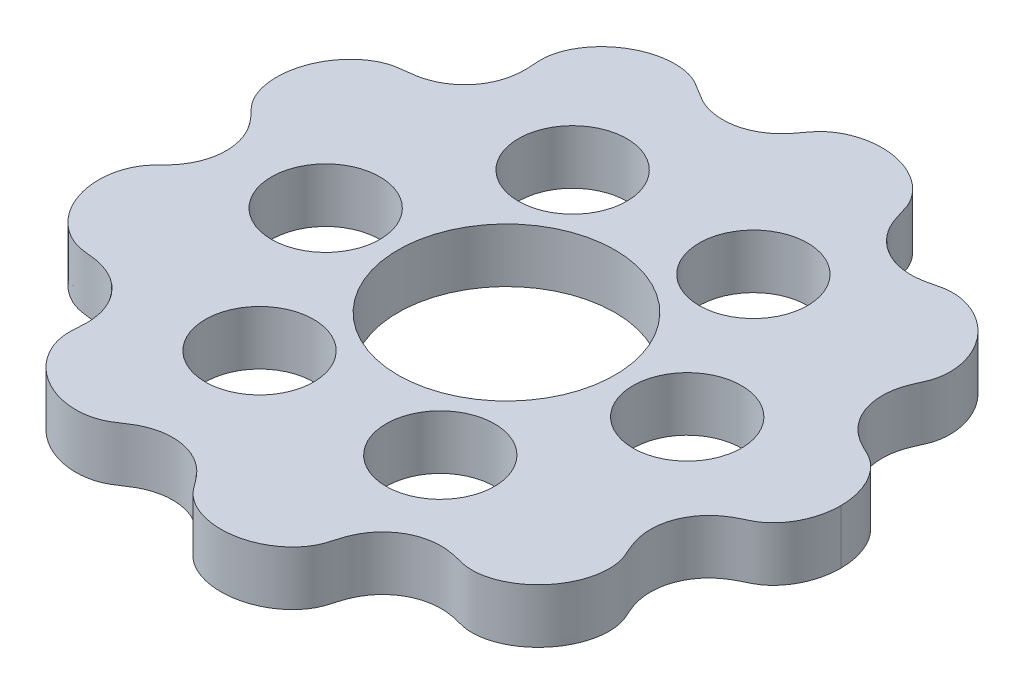
SolidWorks part; units mm, degrees
ref_plane "前视基准面" through (0, 0, 0) normal (0, 0, 1) x (1, 0, 0)
ref_plane "上视基准面" through (0, 0, 0) normal (0, 1, 0) x (1, 0, 0)
ref_plane "右视基准面" through (0, 0, 0) normal (1, 0, 0) x (0, 0, -1)
sketch "草图1" plane through (0, 0, 0) normal (0, 1, 0) x (1, 0, 0)
  circle A0 centre (10, 0) radius 3
  circle A1 centre (5, 8.6603) radius 3
  circle A2 centre (-5, 8.6603) radius 3
  circle A3 centre (-10, 0) radius 3
  circle A4 centre (-5, -8.6603) radius 3
  circle A5 centre (5, -8.6603) radius 3
  circle A6 centre (0, 0) radius 6
  spline S2 degree 3 poles (-15.5, 0.011) (-15.4991, -0.2474) (-15.5295, -0.4891) (-15.6305, -0.9323) (-15.6966, -1.1169) (-15.8274, -1.4223) (-15.8941, -1.5468) (-16.0615, -1.8321) (-16.1502, -1.9501) (-16.294, -2.1344) (-16.35, -2.199) (-16.4452, -2.3062) (-16.4827, -2.3465) (-16.549, -2.4168) (-16.5763, -2.4451) (-16.6255, -2.4958) (-16.6468, -2.5176) (-16.6852, -2.557) (-16.7027, -2.575) (-16.7501, -2.6239) (-16.7768, -2.6517) (-16.8523, -2.7322) (-16.8929, -2.7778) (-16.9689, -2.8679) (-17.0036, -2.9118) (-17.1158, -3.0628) (-17.1867, -3.1746) (-17.316, -3.4165) (-17.3739, -3.5459) (-17.5237, -3.9556) (-17.591, -4.2567) (-17.6669, -5.0909) (-17.6056, -5.6442) (-17.2735, -6.6868) (-17.0025, -7.1771) (-16.3143, -7.9884) (-15.8962, -8.3081) (-15.4173, -8.5299) (-15.3617, -8.5536) (-15.195, -8.6185) (-15.0848, -8.6534) (-14.9332, -8.6908) (-14.8937, -8.6996) (-14.7719, -8.7239) (-14.6902, -8.7368) (-14.5398, -8.7544) (-14.4959, -8.7591) (-14.3852, -8.7703) (-14.3217, -8.7762) (-14.1648, -8.7937) (-14.0931, -8.8018) (-13.932, -8.8263) (-13.8638, -8.8374) (-13.704, -8.87) (-13.6223, -8.8882) (-13.4132, -8.9463) (-13.292, -8.9838) (-12.9849, -9.1087) (-12.8028, -9.1943) (-12.4559, -9.4177) (-12.3042, -9.5314) (-12.0615, -9.7543) (-11.9646, -9.8547) (-11.7359, -10.1278) (-11.6244, -10.2932) (-11.4606, -10.5864) (-11.4015, -10.7131) (-11.3083, -10.9448) (-11.273, -11.0515) (-11.2007, -11.3042) (-11.1742, -11.4381) (-11.1285, -11.7253) (-11.1198, -11.8584) (-11.1107, -12.0688) (-11.1111, -12.1512) (-11.1135, -12.2864) (-11.1159, -12.342) (-11.1205, -12.4352) (-11.1231, -12.4758) (-11.1301, -12.58) (-11.1341, -12.6324) (-11.1439, -12.7633) (-11.1479, -12.8232) (-11.1534, -12.9331) (-11.1548, -12.9808) (-11.156, -13.1242) (-11.1523, -13.2129) (-11.1356, -13.3933) (-11.1226, -13.4837) (-11.0612, -13.7976) (-10.9881, -14.0267) (-10.6784, -14.7131) (-10.3504, -15.1578) (-9.529, -15.8895) (-9.036, -16.1775) (-7.9943, -16.5344) (-7.4449, -16.6024) (-6.7604, -16.5419) (-6.5865, -16.5121) (-6.3591, -16.4535) (-6.2975, -16.4355) (-6.1171, -16.3761) (-6.0036, -16.33) (-5.8229, -16.2417) (-5.7542, -16.2045) (-5.633, -16.1316) (-5.584, -16.1006) (-5.4817, -16.0328) (-5.4341, -16.0003) (-5.3255, -15.9263) (-5.275, -15.8917) (-5.1589, -15.8157) (-5.1072, -15.7823) (-4.9698, -15.699) (-4.8834, -15.6482) (-4.6836, -15.547) (-4.5837, -15.4995) (-4.3435, -15.4044) (-4.1963, -15.3526) (-3.8767, -15.2751) (-3.72, -15.2458) (-3.3969, -15.2164) (-3.2407, -15.212) (-2.961, -15.2265) (-2.8373, -15.2397) (-2.4558, -15.3046) (-2.2224, -15.376) (-1.8022, -15.5518) (-1.6312, -15.6488) (-1.352, -15.8308) (-1.2404, -15.9182) (-0.985, -16.1351) (-0.8834, -16.2441) (-0.7254, -16.4194) (-0.6714, -16.4862) (-0.582, -16.5991) (-0.5488, -16.6431) (-0.491, -16.7209) (-0.468, -16.7526) (-0.4265, -16.81) (-0.4087, -16.8347) (-0.3765, -16.8794) (-0.3618, -16.8998) (-0.322, -16.9548) (-0.299, -16.9861) (-0.2564, -17.0429) (-0.237, -17.0683) (-0.1638, -17.1612) (-0.1143, -17.219) (-0.0103, -17.3308) (0.0434, -17.3838) (0.2374, -17.5597) (0.3928, -17.6747) (0.7375, -17.8804) (0.9261, -17.9706) (1.5922, -18.2172) (2.1194, -18.3002) (3.1771, -18.2588) (3.7076, -18.1351) (4.6649, -17.7078) (5.0915, -17.4031) (5.5212, -16.9383) (5.6155, -16.8203) (5.7354, -16.646) (5.7702, -16.5915) (5.8676, -16.4271) (5.9228, -16.3173) (5.9973, -16.139) (6.0215, -16.0748) (6.0627, -15.9515) (6.0794, -15.8976) (6.113, -15.7821) (6.1275, -15.7306) (6.162, -15.6081) (6.179, -15.5474) (6.2207, -15.4107) (6.2402, -15.3484) (6.2947, -15.1912) (6.3299, -15.0936) (6.4211, -14.8872) (6.4615, -14.8015) (6.5729, -14.5951) (6.6517, -14.4617) (6.847, -14.1957) (6.9499, -14.07) (7.1828, -13.836) (7.3014, -13.7312) (7.5274, -13.5618) (7.6311, -13.4925) (7.9663, -13.2977) (8.1905, -13.2036) (8.6556, -13.0602) (8.8709, -13.0254) (9.2324, -12.9902) (9.3796, -12.9899) (9.6193, -12.9983) (9.7194, -13.0078) (10.0086, -13.0421) (10.1314, -13.0698) (10.321, -13.1117) (10.3859, -13.128) (10.4962, -13.1557) (10.5393, -13.1668) (10.6723, -13.2004) (10.7362, -13.2157) (10.8574, -13.2418) (10.9113, -13.2519) (11.0742, -13.2778) (11.1792, -13.288) (11.3968, -13.296) (11.5081, -13.2935) (11.9671, -13.2559) (12.3335, -13.1635) (13.0433, -12.8551) (13.3861, -12.6398) (13.9997, -12.1127) (14.2707, -11.801) (14.7616, -11.0354) (14.9524, -10.5646) (15.1204, -9.7223) (15.1321, -9.3512) (15.0759, -8.9387) (15.0625, -8.8639) (15.0246, -8.6928) (14.9982, -8.5985) (14.9438, -8.4395) (14.9201, -8.3771) (14.8708, -8.2589) (14.8495, -8.21) (14.8004, -8.1005) (14.7755, -8.0461) (14.7248, -7.9318) (14.7042, -7.885) (14.6611, -7.7823) (14.6379, -7.7257) (14.5844, -7.5842) (14.5512, -7.4925) (14.4889, -7.2807) (14.4607, -7.1748) (14.4095, -6.9133) (14.384, -6.7472) (14.3694, -6.4088) (14.3707, -6.2569) (14.4022, -5.933) (14.4299, -5.7674) (14.5013, -5.489) (14.5373, -5.3743) (14.6229, -5.1485) (14.6706, -5.042) (14.8248, -4.7398) (14.9458, -4.5587) (15.1751, -4.2675) (15.2842, -4.1535) (15.5238, -3.9267) (15.6387, -3.8381) (15.8357, -3.6959) (15.9132, -3.6467) (16.0489, -3.5638) (16.1037, -3.5329) (16.2, -3.48) (16.2418, -3.4581) (16.3659, -3.3942) (16.4292, -3.3638) (16.5335, -3.3134) (16.5741, -3.294) (16.6458, -3.2591) (16.6769, -3.2437) (16.7341, -3.2148) (16.7599, -3.2014) (16.8502, -3.1533) (16.9067, -3.1207) (17.016, -3.0526) (17.0684, -3.0173) (17.2229, -2.9051) (17.3223, -2.8217) (17.6238, -2.53) (17.8129, -2.2881) (18.2209, -1.5858) (18.3927, -1.0808) (18.4876, -0.3727) (18.5, -0.1863) (18.5, 0) knots 72.028512 72.028512 72.028512 72.028512 72.074078 72.074078 72.119645 72.119645 72.165212 72.165212 72.248848 72.248848 72.332485 72.332485 72.416121 72.416121 72.499758 72.499758 72.583394 72.583394 72.667031 72.667031 72.834304 72.834304 73.189471 73.189471 73.544639 73.544639 74.389918 74.389918 75.235196 75.235196 76.925753 76.925753 79.739378 79.739378 82.553002 82.553002 85.366627 85.366627 85.735718 85.735718 86.473899 86.473899 86.732156 86.732156 87.248669 87.248669 87.435753 87.435753 87.622836 87.622836 87.739343 87.739343 87.806817 87.806817 87.862282 87.862282 87.917746 87.917746 87.973211 87.973211 88.010338 88.010338 88.035835 88.035835 88.073035 88.073035 88.101763 88.101763 88.130491 88.130491 88.176029 88.176029 88.248725 88.248725 88.321421 88.321421 88.394116 88.394116 88.466812 88.466812 88.612203 88.612203 88.885531 88.885531 89.158859 89.158859 89.737411 89.737411 90.315962 90.315962 91.721248 91.721248 94.57466 94.57466 97.428072 97.428072 100.281484 100.281484 101.299279 101.299279 101.689637 101.689637 102.470354 102.470354 102.973422 102.973422 103.292551 103.292551 103.517177 103.517177 103.662286 103.662286 103.750882 103.750882 103.839478 103.839478 103.896331 103.896331 103.949341 103.949341 103.988015 103.988015 104.018243 104.018243 104.041011 104.041011 104.086547 104.086547 104.132083 104.132083 104.177618 104.177618 104.262275 104.262275 104.346932 104.346932 104.431589 104.431589 104.516246 104.516246 104.600903 104.600903 104.68556 104.68556 104.854874 104.854874 105.024188 105.024188 105.509561 105.509561 105.994934 105.994934 107.167635 107.167635 108.340335 108.340335 111.071116 111.071116 113.801897 113.801897 116.532678 116.532678 117.415244 117.415244 117.811281 117.811281 118.603356 118.603356 119.037003 119.037003 119.337474 119.337474 119.536725 119.536725 119.679867 119.679867 119.767587 119.767587 119.855307 119.855307 119.902476 119.902476 119.955321 119.955321 119.994755 119.994755 120.025341 120.025341 120.048111 120.048111 120.093651 120.093651 120.145787 120.145787 120.197923 120.197923 120.250058 120.250058 120.385071 120.385071 120.520085 120.520085 120.655098 120.655098 120.988095 120.988095 121.321092 121.321092 122.009977 122.009977 122.698861 122.698861 124.789874 124.789874 126.880887 126.880887 128.9719 128.9719 131.572457 131.572457 133.656669 133.656669 134.131639 134.131639 134.768707 134.768707 135.175769 135.175769 135.425743 135.425743 135.608351 135.608351 135.702641 135.702641 135.778378 135.778378 135.85891 135.85891 135.913634 135.913634 135.968358 135.968358 136.003972 136.003972 136.036178 136.036178 136.057582 136.057582 136.078987 136.078987 136.121797 136.121797 136.164606 136.164606 136.225297 136.225297 136.285987 136.285987 136.346677 136.346677 136.407368 136.407368 136.559502 136.559502 136.711636 136.711636 136.86377 136.86377 137.015904 137.015904 137.421919 137.421919 137.827933 137.827933 138.639962 138.639962 140.372256 140.372256 143.10061 143.10061 144.058319 144.058319 144.058319 144.058319
  spline S3 degree 3 poles (18.5, 0) (18.5, 0.2122) (18.4839, 0.4245) (18.3881, 1.0508) (18.2601, 1.4544) (17.8987, 2.1759) (17.665, 2.4931) (17.3428, 2.801) (17.2786, 2.857) (17.1312, 2.9742) (17.0479, 3.0329) (16.9322, 3.1048) (16.9046, 3.1213) (16.8182, 3.1709) (16.7574, 3.2034) (16.637, 3.2635) (16.5898, 3.2864) (16.4665, 3.3458) (16.3912, 3.3809) (16.2223, 3.4683) (16.1698, 3.496) (16.0551, 3.5606) (15.9889, 3.5992) (15.8215, 3.7062) (15.7094, 3.7815) (15.4507, 3.9931) (15.3061, 4.1225) (15.0585, 4.4109) (14.9645, 4.5334) (14.7807, 4.8223) (14.6964, 4.98) (14.5749, 5.2683) (14.5314, 5.3915) (14.4633, 5.6283) (14.4372, 5.7445) (14.3895, 6.0242) (14.3763, 6.1838) (14.3697, 6.4648) (14.3756, 6.5888) (14.3958, 6.8102) (14.4101, 6.9074) (14.4627, 7.1998) (14.5048, 7.3408) (14.5693, 7.5426) (14.5956, 7.6142) (14.6406, 7.7321) (14.661, 7.7819) (14.7125, 7.9049) (14.7391, 7.9642) (14.7836, 8.0636) (14.8013, 8.1026) (14.8326, 8.1724) (14.846, 8.2024) (14.87, 8.2576) (14.8809, 8.2831) (14.9126, 8.3592) (14.9308, 8.4061) (14.9851, 8.5554) (15.0145, 8.6541) (15.0628, 8.8598) (15.0813, 8.966) (15.1276, 9.369) (15.1181, 9.6875) (14.9764, 10.5005) (14.7828, 10.9983) (14.2149, 11.892) (13.841, 12.2884) (12.9901, 12.9008) (12.5123, 13.1159) (11.8984, 13.2522) (11.7522, 13.2741) (11.5389, 13.2906) (11.4691, 13.2935) (11.2627, 13.2944) (11.131, 13.2851) (10.943, 13.2574) (10.8893, 13.2479) (10.7898, 13.2275) (10.7463, 13.2178) (10.6635, 13.198) (10.6273, 13.189) (10.541, 13.1672) (10.4915, 13.1545) (10.3856, 13.128) (10.3384, 13.1163) (10.2209, 13.0893) (10.149, 13.0733) (9.9949, 13.045) (9.9241, 13.0332) (9.7328, 13.0084) (9.5962, 12.9938) (9.2525, 12.9907) (9.0531, 12.998) (8.5583, 13.0842) (8.253, 13.17) (7.8201, 13.3803) (7.6853, 13.4579) (7.4429, 13.6209) (7.3323, 13.7073) (7.0845, 13.9264) (6.9635, 14.0574) (6.7692, 14.2955) (6.6936, 14.4048) (6.5697, 14.6011) (6.5231, 14.6853) (6.4449, 14.8368) (6.4134, 14.9044) (6.3472, 15.0546) (6.3186, 15.1285) (6.2717, 15.256) (6.2544, 15.3072) (6.2241, 15.3999) (6.2122, 15.4383) (6.1911, 15.5081) (6.182, 15.5392) (6.1584, 15.6207) (6.146, 15.6649) (6.1141, 15.7783) (6.0984, 15.833) (6.0691, 15.9307) (6.0557, 15.9728) (6.0167, 16.088) (5.9909, 16.1556) (5.9046, 16.3576) (5.8358, 16.4877) (5.6707, 16.7463) (5.5749, 16.8735) (5.1553, 17.3486) (4.7417, 17.6588) (3.8055, 18.1036) (3.2833, 18.2392) (2.2347, 18.3082) (1.7082, 18.2411) (0.8939, 17.9691) (0.5812, 17.8072) (0.243, 17.5581) (0.1701, 17.4986) (0.061, 17.3998) (0.022, 17.3623) (-0.0779, 17.2601) (-0.1359, 17.1948) (-0.2283, 17.0798) (-0.2603, 17.0382) (-0.3153, 16.9639) (-0.3346, 16.9374) (-0.3788, 16.8764) (-0.4034, 16.842) (-0.4661, 16.7551) (-0.5034, 16.7034) (-0.5942, 16.5835) (-0.6414, 16.5221) (-0.7506, 16.392) (-0.7993, 16.3359) (-0.921, 16.2065) (-0.9998, 16.1268) (-1.196, 15.9536) (-1.3197, 15.8528) (-1.5945, 15.6722) (-1.7284, 15.5938) (-2.0214, 15.4564) (-2.1723, 15.3974) (-2.4489, 15.3147) (-2.5728, 15.285) (-2.8312, 15.2404) (-2.9569, 15.2268) (-3.3229, 15.2076) (-3.5561, 15.225) (-3.9426, 15.2859) (-4.1014, 15.3279) (-4.3684, 15.4127) (-4.4723, 15.454) (-4.6516, 15.5316) (-4.7247, 15.5674) (-4.8466, 15.6302) (-4.8993, 15.6594) (-5.0145, 15.7254) (-5.0676, 15.7581) (-5.16, 15.8163) (-5.1966, 15.8403) (-5.2628, 15.8841) (-5.2903, 15.9026) (-5.3676, 15.9549) (-5.4073, 15.9821) (-5.4774, 16.0297) (-5.5072, 16.0497) (-5.5618, 16.0857) (-5.5869, 16.102) (-5.6626, 16.1499) (-5.7092, 16.1778) (-5.8532, 16.2587) (-5.9484, 16.3047) (-6.1502, 16.3878) (-6.2556, 16.424) (-6.6897, 16.5449) (-7.0534, 16.5852) (-7.8027, 16.5488) (-8.1874, 16.4725) (-9.0808, 16.1555) (-9.5741, 15.859) (-10.3904, 15.1112) (-10.7128, 14.6588) (-10.9686, 14.0617) (-11.0155, 13.9283) (-11.0734, 13.7202) (-11.0912, 13.6447) (-11.1347, 13.4203) (-11.1505, 13.276) (-11.1556, 13.0775) (-11.1557, 13.029) (-11.1532, 12.929) (-11.151, 12.8777) (-11.1449, 12.7794) (-11.142, 12.7384) (-11.1346, 12.6379) (-11.13, 12.5803) (-11.1215, 12.4504) (-11.118, 12.3947) (-11.1123, 12.247) (-11.1096, 12.1585) (-11.1163, 11.9019) (-11.122, 11.7397) (-11.1905, 11.3545) (-11.2263, 11.1945) (-11.332, 10.8798) (-11.388, 10.7387) (-11.5537, 10.4079) (-11.6664, 10.2248) (-11.88, 9.9522) (-11.9615, 9.8597) (-12.1248, 9.6937) (-12.2083, 9.6178) (-12.4204, 9.4436) (-12.5491, 9.3547) (-12.7845, 9.2117) (-12.8928, 9.1558) (-13.0913, 9.0639) (-13.1814, 9.028) (-13.4625, 8.9262) (-13.6069, 8.8919) (-13.815, 8.8464) (-13.8906, 8.8332) (-14.0154, 8.8132) (-14.0689, 8.806) (-14.2016, 8.789) (-14.2664, 8.7824) (-14.3748, 8.7712) (-14.4175, 8.767) (-14.4937, 8.7593) (-14.5263, 8.7558) (-14.5863, 8.749) (-14.6138, 8.7457) (-14.6959, 8.735) (-14.7458, 8.7274) (-14.9003, 8.7) (-14.9984, 8.6767) (-15.1967, 8.6173) (-15.2957, 8.5815) (-15.6314, 8.4376) (-15.8683, 8.2983) (-16.476, 7.8292) (-16.8192, 7.4349) (-17.3381, 6.5337) (-17.5146, 6.0269) (-17.6673, 5.0006) (-17.6428, 4.4809) (-17.4719, 3.8004) (-17.3989, 3.5976) (-17.2828, 3.3545) (-17.2536, 3.2984) (-17.162, 3.1352) (-17.0959, 3.0343) (-16.981, 2.8826) (-16.9375, 2.8293) (-16.8695, 2.7521) (-16.8505, 2.731) (-16.7947, 2.6704) (-16.7556, 2.6295) (-16.665, 2.5363) (-16.6221, 2.4927) (-16.5295, 2.3961) (-16.4925, 2.3573) (-16.4087, 2.2655) (-16.3659, 2.2177) (-16.2732, 2.1071) (-16.2273, 2.0505) (-16.1237, 1.9121) (-16.0608, 1.8236) (-15.927, 1.6066) (-15.8508, 1.4718) (-15.7179, 1.1697) (-15.6605, 1.0179) (-15.5742, 0.6996) (-15.5427, 0.5448) (-15.5087, 0.2647) (-15.5005, 0.1403) (-15.5, 0.011) knots 0 0 0 0 1.090932 1.090932 3.272797 3.272797 5.454662 5.454662 5.982975 5.982975 6.641919 6.641919 6.841906 6.841906 7.241881 7.241881 7.44968 7.44968 7.657479 7.657479 7.729133 7.729133 7.792125 7.792125 7.864806 7.864806 7.925552 7.925552 7.959669 7.959669 7.993787 7.993787 8.01637 8.01637 8.038954 8.038954 8.071841 8.071841 8.104727 8.104727 8.137614 8.137614 8.218999 8.218999 8.285929 8.285929 8.35286 8.35286 8.486721 8.486721 8.620581 8.620581 8.754442 8.754442 8.888303 8.888303 9.180615 9.180615 9.853154 9.853154 10.525692 10.525692 12.324971 12.324971 15.056526 15.056526 17.788081 17.788081 20.519636 20.519636 21.384038 21.384038 21.812997 21.812997 22.670915 22.670915 23.006767 23.006767 23.240908 23.240908 23.395554 23.395554 23.550201 23.550201 23.645926 23.645926 23.741651 23.741651 23.799337 23.799337 23.872913 23.872913 23.934488 23.934488 23.996064 23.996064 24.022839 24.022839 24.049614 24.049614 24.088163 24.088163 24.126712 24.126712 24.16526 24.16526 24.203809 24.203809 24.264024 24.264024 24.324238 24.324238 24.384452 24.384452 24.444666 24.444666 24.565095 24.565095 24.803479 24.803479 25.041863 25.041863 25.50022 25.50022 26.441035 26.441035 27.38185 27.38185 30.089226 30.089226 32.796601 32.796601 35.503977 35.503977 37.474461 37.474461 38.05942 38.05942 38.405996 38.405996 38.972119 38.972119 39.254764 39.254764 39.38971 39.38971 39.524657 39.524657 39.659604 39.659604 39.757663 39.757663 39.814731 39.814731 39.871799 39.871799 39.925119 39.925119 39.962421 39.962421 39.993717 39.993717 40.016824 40.016824 40.039931 40.039931 40.086144 40.086144 40.132357 40.132357 40.178571 40.178571 40.224784 40.224784 40.270997 40.270997 40.342859 40.342859 40.414721 40.414721 40.486583 40.486583 40.635615 40.635615 40.784648 40.784648 40.93368 40.93368 41.259137 41.259137 41.950599 41.950599 42.642061 42.642061 44.674854 44.674854 46.707646 46.707646 49.582966 49.582966 52.458286 52.458286 53.280645 53.280645 53.753504 53.753504 54.699222 54.699222 54.996403 54.996403 55.270206 55.270206 55.434984 55.434984 55.599762 55.599762 55.696667 55.696667 55.793572 55.793572 55.890476 55.890476 55.941196 55.941196 55.975652 55.975652 56.016335 56.016335 56.037813 56.037813 56.059291 56.059291 56.091585 56.091585 56.123879 56.123879 56.156173 56.156173 56.237966 56.237966 56.304944 56.304944 56.371923 56.371923 56.50588 56.50588 56.639836 56.639836 56.773793 56.773793 56.90775 56.90775 57.201674 57.201674 57.860341 57.860341 58.519008 58.519008 60.089967 60.089967 62.780354 62.780354 65.47074 65.47074 68.161126 68.161126 69.401907 69.401907 69.789761 69.789761 70.565471 70.565471 70.999232 70.999232 71.154269 71.154269 71.419837 71.419837 71.600923 71.600923 71.695548 71.695548 71.771019 71.771019 71.826907 71.826907 71.882795 71.882795 71.935749 71.935749 71.975182 71.975182 72.005728 72.005728 72.028512 72.028512 72.028512 72.028512
  dimension "D1" = 6
  dimension "D2" = 12
extrude "凸台-拉伸1" add sketch "草图1" along normal blind 3
